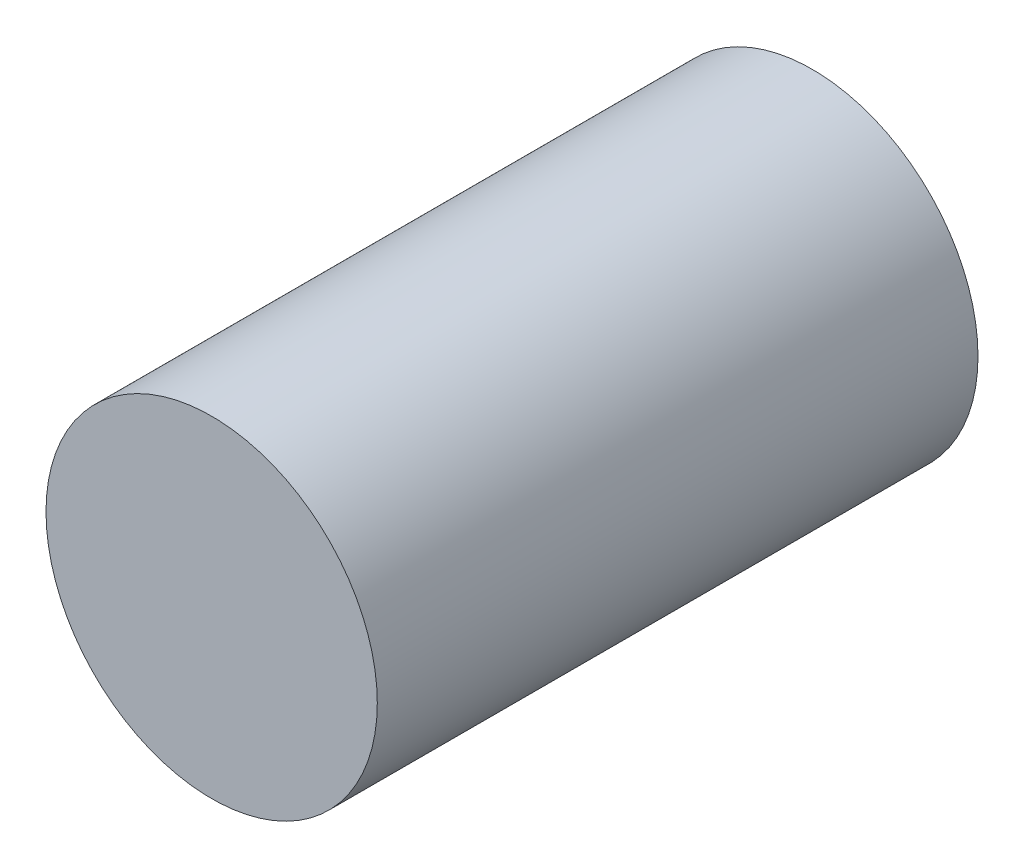
SolidWorks part; units mm, degrees
ref_plane "Front Plane" through (0, 0, 0) normal (0, 0, 1) x (1, 0, 0)
ref_plane "Top Plane" through (0, 0, 0) normal (0, 1, 0) x (1, 0, 0)
ref_plane "Right Plane" through (0, 0, 0) normal (1, 0, 0) x (0, 0, -1)
sketch "Sketch1" plane through (0, 0, 0) normal (0, 0, 1) x (1, 0, 0)
  circle A0 centre (-5.1705, -0.7286) radius 4.95
extrude "Boss-Extrude1" add sketch "Sketch1" along normal blind 17.95
